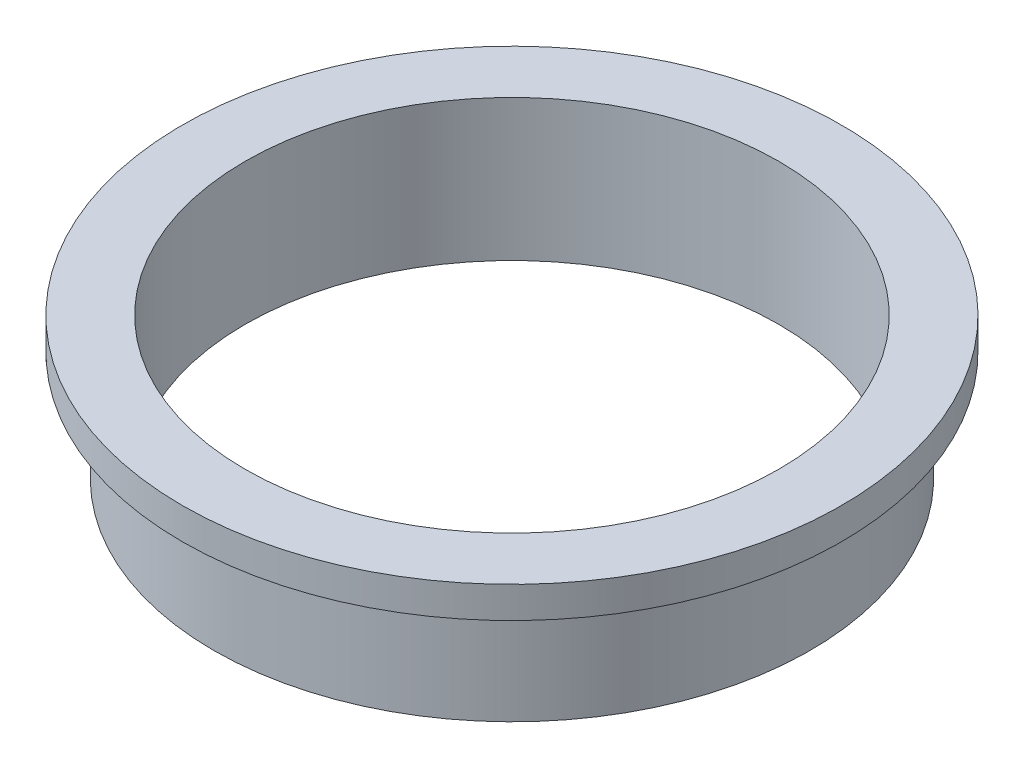
SolidWorks part; units mm, degrees
ref_plane "Alzado" through (0, 0, 0) normal (0, 0, 1) x (1, 0, 0)
ref_plane "Planta" through (0, 0, 0) normal (0, 1, 0) x (1, 0, 0)
ref_plane "Vista lateral" through (0, 0, 0) normal (1, 0, 0) x (0, 0, -1)
sketch "Croquis1" plane through (0, 0, 0) normal (0, 1, 0) x (1, 0, 0)
  circle A0 centre (0, 0) radius 9.5
  circle A1 centre (0, 0) radius 8.5
  dimension "D1" = 19
  dimension "D2" = 17
extrude "Saliente-Extruir1" add sketch "Croquis1" along normal blind 4.5
sketch "Croquis2" plane through (0, 4.5, 0) normal (0, 1, 0) x (1, 0, 0)
  circle A0 centre (0, 0) radius 10.5
  circle A1 centre (0, 0) radius 8.5 construction
  circle A2 centre (0, 0) radius 8.5
  dimension "D1" = 21
extrude "Saliente-Extruir2" add sketch "Croquis2" against normal blind 1
